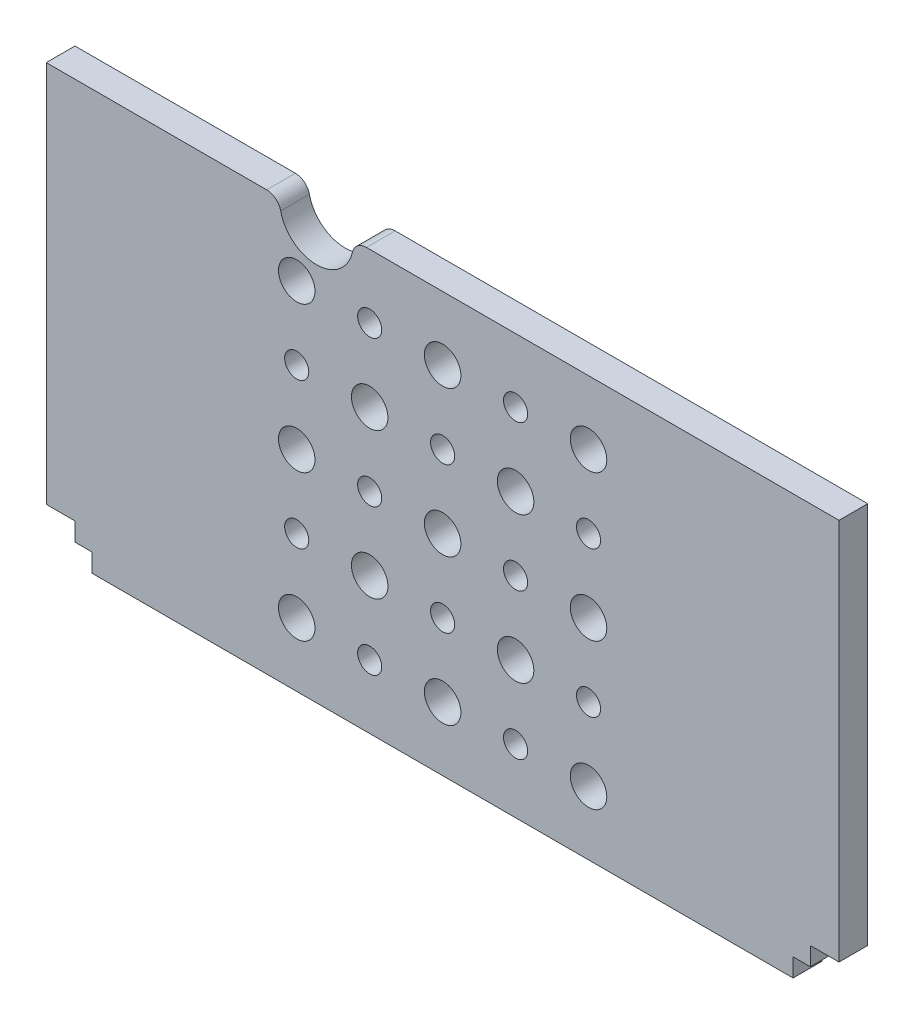
SolidWorks part; units mm, degrees
ref_plane "Front Plane" through (0, 0, 0) normal (0, 0, 1) x (1, 0, 0)
ref_plane "Top Plane" through (0, 0, 0) normal (0, 1, 0) x (1, 0, 0)
ref_plane "Right Plane" through (0, 0, 0) normal (1, 0, 0) x (0, 0, -1)
sketch "Sketch1" plane through (0, 0, 0) normal (0, 0, 1) x (1, 0, 0)
  line L13 (-30.6337, 36.5) -> (-69, 36.5)
  line L14 (-69, 36.5) -> (-69, -30.1)
  line L15 (-69, -30.1) -> (-64, -30.1)
  line L16 (-64, -30.1) -> (-64, -33.3)
  line L17 (-64, -33.3) -> (-61, -33.3)
  line L18 (-61, -33.3) -> (-61, -36.5)
  line L19 (-61, -36.5) -> (61, -36.5)
  line L20 (61, -36.5) -> (61, -33.3)
  line L21 (61, -33.3) -> (64, -33.3)
  line L22 (64, -33.3) -> (64, -30.1)
  line L23 (64, -30.1) -> (69, -30.1)
  line L24 (69, -30.1) -> (69, 36.5)
  line L25 (69, 36.5) -> (-13.2663, 36.5)
  line L26 (-30.6337, 36.5) -> (-69, 36.5)
  line L27 (-69, 36.5) -> (-69, -30.1)
  line L28 (-69, -30.1) -> (-64, -30.1)
  line L29 (-64, -30.1) -> (-64, -33.3)
  line L30 (-64, -33.3) -> (-61, -33.3)
  line L31 (-61, -33.3) -> (-61, -36.5)
  line L32 (-61, -36.5) -> (61, -36.5)
  line L33 (61, -36.5) -> (61, -33.3)
  line L34 (61, -33.3) -> (64, -33.3)
  line L35 (64, -33.3) -> (64, -30.1)
  line L36 (64, -30.1) -> (69, -30.1)
  line L37 (69, -30.1) -> (69, 36.5)
  line L38 (69, 36.5) -> (-13.2663, 36.5)
  arc A1 (-10.6, 25.4) -> (-14.8, 25.4) centre (-12.7, 25.4) ccw construction
  arc A2 (3.175, -25.4) -> (-3.175, -25.4) centre (0, -25.4) ccw
  arc A3 (-13.2663, 36.5) -> (-15.7055, 34.5478) centre (-13.2663, 34) ccw
  arc A4 (-28.1945, 34.5478) -> (-15.7055, 34.5478) centre (-21.95, 35.95) ccw
  arc A5 (-28.1945, 34.5478) -> (-30.6337, 36.5) centre (-30.6337, 34) ccw
  arc A6 (-13.2663, 36.5) -> (-15.7055, 34.5478) centre (-13.2663, 34) ccw
  arc A7 (-28.1945, 34.5478) -> (-15.7055, 34.5478) centre (-21.95, 35.95) ccw
  arc A8 (-28.1945, 34.5478) -> (-30.6337, 36.5) centre (-30.6337, 34) ccw
  arc A9 (-3.175, -25.4) -> (3.175, -25.4) centre (0, -25.4) ccw
  arc A10 (3.175, -25.4) -> (-3.175, -25.4) centre (0, -25.4) ccw
  arc A11 (-3.175, -25.4) -> (3.175, -25.4) centre (0, -25.4) ccw
  arc A12 (-3.175, 0) -> (3.175, 0) centre (0, 0) ccw
  arc A13 (3.175, 0) -> (-3.175, 0) centre (0, 0) ccw
  arc A14 (-3.175, 0) -> (3.175, 0) centre (0, 0) ccw
  arc A15 (3.175, 0) -> (-3.175, 0) centre (0, 0) ccw
  arc A16 (-22.225, -25.4) -> (-28.575, -25.4) centre (-25.4, -25.4) ccw
  arc A17 (-28.575, -25.4) -> (-22.225, -25.4) centre (-25.4, -25.4) ccw
  arc A18 (-22.225, -25.4) -> (-28.575, -25.4) centre (-25.4, -25.4) ccw
  arc A19 (-28.575, -25.4) -> (-22.225, -25.4) centre (-25.4, -25.4) ccw
  arc A20 (28.575, -25.4) -> (22.225, -25.4) centre (25.4, -25.4) ccw
  arc A21 (22.225, -25.4) -> (28.575, -25.4) centre (25.4, -25.4) ccw
  arc A22 (28.575, -25.4) -> (22.225, -25.4) centre (25.4, -25.4) ccw
  arc A23 (22.225, -25.4) -> (28.575, -25.4) centre (25.4, -25.4) ccw
  arc A24 (-9.525, -12.7) -> (-15.875, -12.7) centre (-12.7, -12.7) ccw
  arc A25 (-15.875, -12.7) -> (-9.525, -12.7) centre (-12.7, -12.7) ccw
  arc A26 (-9.525, -12.7) -> (-15.875, -12.7) centre (-12.7, -12.7) ccw
  arc A27 (-15.875, -12.7) -> (-9.525, -12.7) centre (-12.7, -12.7) ccw
  arc A28 (-23.3, -12.7) -> (-27.5, -12.7) centre (-25.4, -12.7) ccw
  arc A29 (-27.5, -12.7) -> (-23.3, -12.7) centre (-25.4, -12.7) ccw
  arc A30 (-23.3, -12.7) -> (-27.5, -12.7) centre (-25.4, -12.7) ccw
  arc A31 (-27.5, -12.7) -> (-23.3, -12.7) centre (-25.4, -12.7) ccw
  arc A32 (14.8, -25.4) -> (10.6, -25.4) centre (12.7, -25.4) ccw
  arc A33 (10.6, -25.4) -> (14.8, -25.4) centre (12.7, -25.4) ccw
  arc A34 (14.8, -25.4) -> (10.6, -25.4) centre (12.7, -25.4) ccw
  arc A35 (10.6, -25.4) -> (14.8, -25.4) centre (12.7, -25.4) ccw
  arc A36 (-10.6, -25.4) -> (-14.8, -25.4) centre (-12.7, -25.4) ccw
  arc A37 (-14.8, -25.4) -> (-10.6, -25.4) centre (-12.7, -25.4) ccw
  arc A38 (-10.6, -25.4) -> (-14.8, -25.4) centre (-12.7, -25.4) ccw
  arc A39 (-14.8, -25.4) -> (-10.6, -25.4) centre (-12.7, -25.4) ccw
  arc A40 (2.1, -12.7) -> (-2.1, -12.7) centre (0, -12.7) ccw
  arc A41 (-2.1, -12.7) -> (2.1, -12.7) centre (0, -12.7) ccw
  arc A42 (2.1, -12.7) -> (-2.1, -12.7) centre (0, -12.7) ccw
  arc A43 (-2.1, -12.7) -> (2.1, -12.7) centre (0, -12.7) ccw
  arc A44 (-22.225, 25.4) -> (-28.575, 25.4) centre (-25.4, 25.4) ccw construction
  arc A45 (-28.575, 25.4) -> (-22.225, 25.4) centre (-25.4, 25.4) ccw construction
  arc A46 (-14.8, 25.4) -> (-10.6, 25.4) centre (-12.7, 25.4) ccw construction
  arc A47 (28.575, 25.4) -> (22.225, 25.4) centre (25.4, 25.4) ccw construction
  arc A48 (22.225, 25.4) -> (28.575, 25.4) centre (25.4, 25.4) ccw construction
  arc A49 (27.5, 12.7) -> (23.3, 12.7) centre (25.4, 12.7) ccw construction
  arc A50 (23.3, 12.7) -> (27.5, 12.7) centre (25.4, 12.7) ccw construction
  arc A51 (28.575, 0) -> (22.225, 0) centre (25.4, 0) ccw construction
  arc A52 (22.225, 0) -> (28.575, 0) centre (25.4, 0) ccw construction
  arc A53 (23.3, -12.7) -> (27.5, -12.7) centre (25.4, -12.7) ccw construction
  arc A54 (27.5, -12.7) -> (23.3, -12.7) centre (25.4, -12.7) ccw construction
  arc A55 (10.6, 0) -> (14.8, 0) centre (12.7, 0) ccw construction
  arc A56 (14.8, 0) -> (10.6, 0) centre (12.7, 0) ccw construction
  arc A57 (9.525, 12.7) -> (15.875, 12.7) centre (12.7, 12.7) ccw construction
  arc A58 (15.875, 12.7) -> (9.525, 12.7) centre (12.7, 12.7) ccw construction
  arc A59 (10.6, 25.4) -> (14.8, 25.4) centre (12.7, 25.4) ccw construction
  arc A60 (14.8, 25.4) -> (10.6, 25.4) centre (12.7, 25.4) ccw construction
  arc A61 (3.175, 25.4) -> (-3.175, 25.4) centre (0, 25.4) ccw construction
  arc A62 (-3.175, 25.4) -> (3.175, 25.4) centre (0, 25.4) ccw construction
  arc A63 (2.1, 12.7) -> (-2.1, 12.7) centre (0, 12.7) ccw construction
  arc A64 (-2.1, 12.7) -> (2.1, 12.7) centre (0, 12.7) ccw construction
  arc A65 (-27.5, 12.7) -> (-23.3, 12.7) centre (-25.4, 12.7) ccw construction
  arc A66 (-23.3, 12.7) -> (-27.5, 12.7) centre (-25.4, 12.7) ccw construction
  arc A67 (-9.525, 12.7) -> (-15.875, 12.7) centre (-12.7, 12.7) ccw construction
  arc A68 (-15.875, 12.7) -> (-9.525, 12.7) centre (-12.7, 12.7) ccw construction
  arc A69 (-10.6, 0) -> (-14.8, 0) centre (-12.7, 0) ccw construction
  arc A70 (-14.8, 0) -> (-10.6, 0) centre (-12.7, 0) ccw construction
  arc A71 (9.525, -12.7) -> (15.875, -12.7) centre (12.7, -12.7) ccw construction
  arc A72 (15.875, -12.7) -> (9.525, -12.7) centre (12.7, -12.7) ccw construction
  arc A73 (-28.575, 0) -> (-22.225, 0) centre (-25.4, 0) ccw construction
  arc A74 (-22.225, 0) -> (-28.575, 0) centre (-25.4, 0) ccw construction
  arc A75 (-10.6, 25.4) -> (-14.8, 25.4) centre (-12.7, 25.4) ccw
  arc A76 (-22.225, 25.4) -> (-28.575, 25.4) centre (-25.4, 25.4) ccw
  arc A77 (-28.575, 25.4) -> (-22.225, 25.4) centre (-25.4, 25.4) ccw
  arc A78 (-14.8, 25.4) -> (-10.6, 25.4) centre (-12.7, 25.4) ccw
  arc A79 (28.575, 25.4) -> (22.225, 25.4) centre (25.4, 25.4) ccw
  arc A80 (22.225, 25.4) -> (28.575, 25.4) centre (25.4, 25.4) ccw
  arc A81 (27.5, 12.7) -> (23.3, 12.7) centre (25.4, 12.7) ccw
  arc A82 (23.3, 12.7) -> (27.5, 12.7) centre (25.4, 12.7) ccw
  arc A83 (28.575, 0) -> (22.225, 0) centre (25.4, 0) ccw
  arc A84 (22.225, 0) -> (28.575, 0) centre (25.4, 0) ccw
  arc A85 (23.3, -12.7) -> (27.5, -12.7) centre (25.4, -12.7) ccw
  arc A86 (27.5, -12.7) -> (23.3, -12.7) centre (25.4, -12.7) ccw
  arc A87 (10.6, 0) -> (14.8, 0) centre (12.7, 0) ccw
  arc A88 (14.8, 0) -> (10.6, 0) centre (12.7, 0) ccw
  arc A89 (9.525, 12.7) -> (15.875, 12.7) centre (12.7, 12.7) ccw
  arc A90 (15.875, 12.7) -> (9.525, 12.7) centre (12.7, 12.7) ccw
  arc A91 (10.6, 25.4) -> (14.8, 25.4) centre (12.7, 25.4) ccw
  arc A92 (14.8, 25.4) -> (10.6, 25.4) centre (12.7, 25.4) ccw
  arc A93 (3.175, 25.4) -> (-3.175, 25.4) centre (0, 25.4) ccw
  arc A94 (-3.175, 25.4) -> (3.175, 25.4) centre (0, 25.4) ccw
  arc A95 (2.1, 12.7) -> (-2.1, 12.7) centre (0, 12.7) ccw
  arc A96 (-2.1, 12.7) -> (2.1, 12.7) centre (0, 12.7) ccw
  arc A97 (-27.5, 12.7) -> (-23.3, 12.7) centre (-25.4, 12.7) ccw
  arc A98 (-23.3, 12.7) -> (-27.5, 12.7) centre (-25.4, 12.7) ccw
  arc A99 (-9.525, 12.7) -> (-15.875, 12.7) centre (-12.7, 12.7) ccw
  arc A100 (-15.875, 12.7) -> (-9.525, 12.7) centre (-12.7, 12.7) ccw
  arc A101 (-10.6, 0) -> (-14.8, 0) centre (-12.7, 0) ccw
  arc A102 (-14.8, 0) -> (-10.6, 0) centre (-12.7, 0) ccw
  arc A103 (9.525, -12.7) -> (15.875, -12.7) centre (12.7, -12.7) ccw
  arc A104 (15.875, -12.7) -> (9.525, -12.7) centre (12.7, -12.7) ccw
  arc A105 (-28.575, 0) -> (-22.225, 0) centre (-25.4, 0) ccw
  arc A106 (-22.225, 0) -> (-28.575, 0) centre (-25.4, 0) ccw
  dimension "D1" = 0
  dimension "D2" = 0
  dimension "D3" = 0
  dimension "D4" = 0
  dimension "D5" = 0
  dimension "D6" = 0
  dimension "D7" = 0
  dimension "D8" = 0
  dimension "D9" = 0
  dimension "D10" = 0
extrude "Boss-Extrude1" add sketch "Sketch1" against normal blind 5
